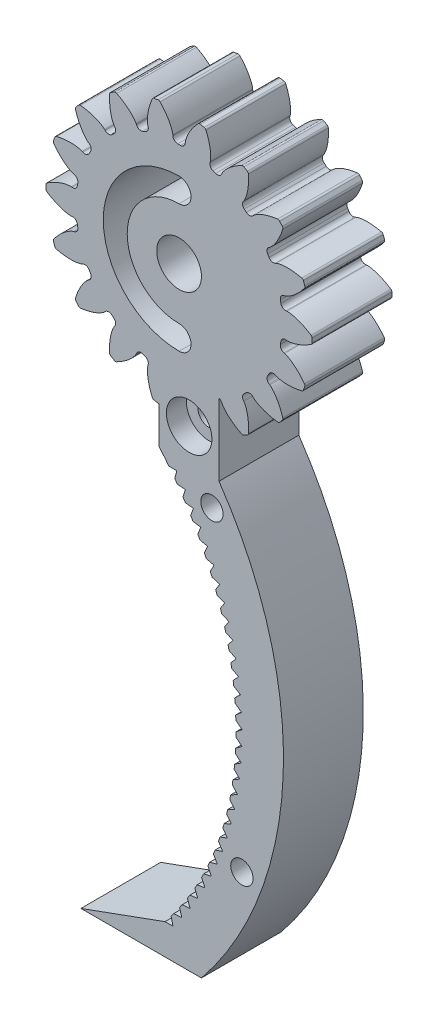
SolidWorks part; units mm, degrees
material "Alloy Steel"
ref_plane "Front" through (0, 0, 0) normal (0, 0, 1) x (1, 0, 0)
ref_plane "Top" through (0, 0, 0) normal (0, 1, 0) x (1, 0, 0)
ref_plane "Right" through (0, 0, 0) normal (1, 0, 0) x (0, 0, -1)
sketch "Sketch1" plane through (0, 0, 0) normal (0, 0, 1) x (1, 0, 0)
  circle A0 centre (0, 0) radius 21.1667
extrude "Boss-Extrude1" add sketch "Sketch1" along normal blind 12.7
sketch "Sketch3" plane through (0, 0, 0) normal (0, 0, 1) x (1, 0, 0)
  line L0 (0, 0) -> (43.7181, 0) construction
  line L2 (0, 0) -> (-0.9393, 16.3773) construction
  line L3 (0, 0) -> (0.9393, 16.3773) construction
  line L4 (0.9393, 16.3773) -> (0.9886, 17.2368) construction
  line L5 (0, 0) -> (0, 61.276) construction
  line L6 (-0.9393, 16.3773) -> (-0.9886, 17.2368) construction
  circle A0 centre (0, 0) radius 21.1667 construction
  circle A1 centre (0, 0) radius 19.05 construction
  circle A2 centre (0, 0) radius 17.2652 construction
  arc A3 (0.9393, 16.3773) -> (-0.9393, 16.3773) centre (0, 0) ccw construction
  arc A5 (3.1554, 20.9302) -> (-3.1554, 20.9302) centre (0, 0) ccw
  spline S0 degree 4 poles (-0.9886, 17.2368) (-0.9891, 17.2432) (-0.9907, 17.2612) (-0.9949, 17.295) (-1.0034, 17.35) (-1.0167, 17.4198) (-1.0366, 17.5096) (-1.0637, 17.6148) (-1.0972, 17.7297) (-1.1377, 17.8539) (-1.1816, 17.977) (-1.2287, 18.099) (-1.2785, 18.2198) (-1.3423, 18.3651) (-1.4236, 18.5381) (-1.5256, 18.738) (-1.6493, 18.9622) (-1.784, 19.1875) (-1.9235, 19.4067) (-2.0724, 19.6249) (-2.2221, 19.8338) (-2.3856, 20.0472) (-2.5406, 20.2425) (-2.7229, 20.4571) (-2.8726, 20.6291) (-3.0791, 20.8514) (-3.2038, 20.9813) (-3.3529, 21.1316) (-3.4207, 21.1975) (-3.4624, 21.2381) knots 0 0 0 0 0 0.005377 0.015084 0.028532 0.04661 0.064855 0.092111 0.119476 0.146842 0.174209 0.201575 0.228941 0.256307 0.307035 0.361767 0.4165 0.471232 0.525964 0.580697 0.635429 0.690161 0.744894 0.799626 0.854358 0.909091 0.954545 1 1 1 1 1 construction
  spline S1 degree 4 poles (-0.9886, 17.2368) (-0.9891, 17.2432) (-0.9907, 17.2612) (-0.9949, 17.295) (-1.0034, 17.35) (-1.0167, 17.4198) (-1.0366, 17.5096) (-1.0637, 17.6148) (-1.0972, 17.7297) (-1.1377, 17.8539) (-1.1816, 17.977) (-1.2287, 18.099) (-1.2785, 18.2198) (-1.3423, 18.3651) (-1.4236, 18.5381) (-1.5256, 18.738) (-1.6493, 18.9622) (-1.784, 19.1875) (-1.9235, 19.4067) (-2.0724, 19.6249) (-2.2221, 19.8338) (-2.3856, 20.0472) (-2.5406, 20.2425) (-2.7229, 20.4571) (-2.8726, 20.6291) (-3.0344, 20.8032) (-3.1141, 20.8874) (-3.1554, 20.9302) knots 0 0 0 0 0 0.005377 0.015084 0.028532 0.04661 0.064855 0.092111 0.119476 0.146842 0.174209 0.201575 0.228941 0.256307 0.307035 0.361767 0.4165 0.471232 0.525964 0.580697 0.635429 0.690161 0.744894 0.799626 0.854358 0.909091 0.909091 0.909091 0.909091 0.909091
  spline S2 degree 4 poles (0.9886, 17.2368) (0.9891, 17.2432) (0.9907, 17.2612) (0.9949, 17.295) (1.0034, 17.35) (1.0167, 17.4198) (1.0366, 17.5096) (1.0637, 17.6148) (1.0972, 17.7297) (1.1377, 17.8539) (1.1816, 17.977) (1.2287, 18.099) (1.2785, 18.2198) (1.3423, 18.3651) (1.4236, 18.5381) (1.5256, 18.738) (1.6493, 18.9622) (1.784, 19.1875) (1.9235, 19.4067) (2.0724, 19.6249) (2.2221, 19.8338) (2.3856, 20.0472) (2.5406, 20.2425) (2.7229, 20.4571) (2.8726, 20.6291) (3.0791, 20.8514) (3.2038, 20.9813) (3.3529, 21.1316) (3.4207, 21.1975) (3.4624, 21.2381) knots 0 0 0 0 0 0.005377 0.015084 0.028532 0.04661 0.064855 0.092111 0.119476 0.146842 0.174209 0.201575 0.228941 0.256307 0.307035 0.361767 0.4165 0.471232 0.525964 0.580697 0.635429 0.690161 0.744894 0.799626 0.854358 0.909091 0.954545 1 1 1 1 1 construction
  spline S3 degree 4 poles (0.9886, 17.2368) (0.9891, 17.2432) (0.9907, 17.2612) (0.9949, 17.295) (1.0034, 17.35) (1.0167, 17.4198) (1.0366, 17.5096) (1.0637, 17.6148) (1.0972, 17.7297) (1.1377, 17.8539) (1.1816, 17.977) (1.2287, 18.099) (1.2785, 18.2198) (1.3423, 18.3651) (1.4236, 18.5381) (1.5256, 18.738) (1.6493, 18.9622) (1.784, 19.1875) (1.9235, 19.4067) (2.0724, 19.6249) (2.2221, 19.8338) (2.3856, 20.0472) (2.5406, 20.2425) (2.7229, 20.4571) (2.8726, 20.6291) (3.0344, 20.8032) (3.1141, 20.8874) (3.1554, 20.9302) knots 0 0 0 0 0 0.005377 0.015084 0.028532 0.04661 0.064855 0.092111 0.119476 0.146842 0.174209 0.201575 0.228941 0.256307 0.307035 0.361767 0.4165 0.471232 0.525964 0.580697 0.635429 0.690161 0.744894 0.799626 0.854358 0.909091 0.909091 0.909091 0.909091 0.909091
  point P0 (0, 16.4042)
sketch "DCLTBC" plane through (0, 0, 0) normal (0, 0, 1) x (1, 0, 0)
  line L0 (0, 0) -> (41.04, 0) construction
  line L1 (-0.9393, 16.3773) -> (-0.9886, 17.2368) construction
  line L2 (0.9393, 16.3773) -> (0.9886, 17.2368) construction
  line L3 (-0.9393, 16.3773) -> (-0.9886, 17.2368)
  line L4 (0.9393, 16.3773) -> (0.9886, 17.2368)
  line L5 (0, 0) -> (0, 104.9356) construction
  circle A0 centre (0, 0) radius 21.1667
  circle A1 centre (0, 0) radius 19.05 construction
  circle A2 centre (0, 0) radius 17.2652 construction
  arc A3 (0.9393, 16.3773) -> (-0.9393, 16.3773) centre (0, 0) ccw construction
  arc A4 (0.9393, 16.3773) -> (-0.9393, 16.3773) centre (0, 0) ccw
  spline S0 degree 4 poles (-998.2859, -55.9585) (-15.2714, 14.5763) (-1.1564, 16.0258) (-0.9033, 16.703) (-1.0034, 17.35) (-1.0167, 17.4198) (-1.0366, 17.5096) (-1.0637, 17.6148) (-1.0972, 17.7297) (-1.1377, 17.8539) (-1.1816, 17.977) (-1.2287, 18.099) (-1.2785, 18.2198) (-1.3423, 18.3651) (-1.4236, 18.5381) (-1.5256, 18.738) (-1.6493, 18.9622) (-1.784, 19.1875) (-1.9235, 19.4067) (-2.0724, 19.6249) (-2.2221, 19.8338) (-2.3856, 20.0472) (-2.5406, 20.2425) (-2.7229, 20.4571) (-3.4042, 21.2399) (-5.6764, 23.4628) (17.3745, -0.7418) (-697.1444, 740.8893) knots -0.501613 -0.501613 -0.501613 -0.501613 -0.501613 0.005377 0.015084 0.028532 0.04661 0.064855 0.092111 0.119476 0.146842 0.174209 0.201575 0.228941 0.256307 0.307035 0.361767 0.4165 0.471232 0.525964 0.580697 0.635429 0.690161 0.744894 0.799626 0.854358 1.68661 1.68661 1.68661 1.68661 1.68661 only from (-0.9886, 17.2368) to (-3.1554, 20.9302) construction
  spline S1 degree 4 poles (998.2859, -55.9585) (15.2714, 14.5763) (1.1564, 16.0258) (0.9033, 16.703) (1.0034, 17.35) (1.0167, 17.4198) (1.0366, 17.5096) (1.0637, 17.6148) (1.0972, 17.7297) (1.1377, 17.8539) (1.1816, 17.977) (1.2287, 18.099) (1.2785, 18.2198) (1.3423, 18.3651) (1.4236, 18.5381) (1.5256, 18.738) (1.6493, 18.9622) (1.784, 19.1875) (1.9235, 19.4067) (2.0724, 19.6249) (2.2221, 19.8338) (2.3856, 20.0472) (2.5406, 20.2425) (2.7229, 20.4571) (3.4042, 21.2399) (5.6764, 23.4628) (-17.3745, -0.7418) (697.1444, 740.8893) knots -0.501613 -0.501613 -0.501613 -0.501613 -0.501613 0.005377 0.015084 0.028532 0.04661 0.064855 0.092111 0.119476 0.146842 0.174209 0.201575 0.228941 0.256307 0.307035 0.361767 0.4165 0.471232 0.525964 0.580697 0.635429 0.690161 0.744894 0.799626 0.854358 1.68661 1.68661 1.68661 1.68661 1.68661 only from (0.9886, 17.2368) to (3.1554, 20.9302) construction
  spline S2 degree 4 poles (-0.9886, 17.2368) (-0.9891, 17.2432) (-0.9907, 17.2612) (-0.9949, 17.295) (-1.0034, 17.35) (-1.0167, 17.4198) (-1.0366, 17.5096) (-1.0637, 17.6148) (-1.0972, 17.7297) (-1.1377, 17.8539) (-1.1816, 17.977) (-1.2287, 18.099) (-1.2785, 18.2198) (-1.3423, 18.3651) (-1.4236, 18.5381) (-1.5256, 18.738) (-1.6493, 18.9622) (-1.784, 19.1875) (-1.9235, 19.4067) (-2.0724, 19.6249) (-2.2221, 19.8338) (-2.3856, 20.0472) (-2.5406, 20.2425) (-2.7229, 20.4571) (-2.8726, 20.6291) (-3.0344, 20.8032) (-3.1141, 20.8874) (-3.1554, 20.9302) knots 0 0 0 0 0 0.005377 0.015084 0.028532 0.04661 0.064855 0.092111 0.119476 0.146842 0.174209 0.201575 0.228941 0.256307 0.307035 0.361767 0.4165 0.471232 0.525964 0.580697 0.635429 0.690161 0.744894 0.799626 0.854358 0.909091 0.909091 0.909091 0.909091 0.909091
  spline S3 degree 4 poles (0.9886, 17.2368) (0.9891, 17.2432) (0.9907, 17.2612) (0.9949, 17.295) (1.0034, 17.35) (1.0167, 17.4198) (1.0366, 17.5096) (1.0637, 17.6148) (1.0972, 17.7297) (1.1377, 17.8539) (1.1816, 17.977) (1.2287, 18.099) (1.2785, 18.2198) (1.3423, 18.3651) (1.4236, 18.5381) (1.5256, 18.738) (1.6493, 18.9622) (1.784, 19.1875) (1.9235, 19.4067) (2.0724, 19.6249) (2.2221, 19.8338) (2.3856, 20.0472) (2.5406, 20.2425) (2.7229, 20.4571) (2.8726, 20.6291) (3.0344, 20.8032) (3.1141, 20.8874) (3.1554, 20.9302) knots 0 0 0 0 0 0.005377 0.015084 0.028532 0.04661 0.064855 0.092111 0.119476 0.146842 0.174209 0.201575 0.228941 0.256307 0.307035 0.361767 0.4165 0.471232 0.525964 0.580697 0.635429 0.690161 0.744894 0.799626 0.854358 0.909091 0.909091 0.909091 0.909091 0.909091
extrude "Cut-Extrude-DCLTBC" cut sketch "DCLTBC" along normal through all
fillet "Fillet-Tip-DCLTBC" radius 0.3764 2 edges at (3.1554, 20.9302, 6.35) (-3.1554, 20.9302, 6.35)
fillet "Fillet-Root-DCLTBC" radius 0.7528 2 edges at (-0.9393, 16.3773, 6.35) (0.9393, 16.3773, 6.35)
pattern_circular "CirPattern-DCLTBC" count 18 over 360 about axis through (0, 0, 12.7) along (0, 0, 1) of "Cut-Extrude-DCLTBC", "Fillet-Tip-DCLTBC", "Fillet-Root-DCLTBC"
sketch "DCGTBC" [suppressed] plane through (0, 0, 0) normal (0, 0, 1) x (1, 0, 0)
  line L0 (0, 0) -> (41.04, 0) construction
  line L1 (-22.6634, 1.9828) -> (0, 0) construction
  line L2 (0, 0) -> (22.6634, 1.9828) construction
  line L3 (0, 0) -> (-16.5124, 0)
  line L5 (0, 0) -> (0, 104.9356) construction
  circle A0 centre (0, 0) radius 25
  circle A1 centre (0, 0) radius 24 construction
  circle A2 centre (0, 0) radius 21.7514 construction
  arc A3 (0.0626, 22.7499) -> (-0.0626, 22.7499) centre (0, 0) ccw construction
  arc A11 (22.6634, 1.9828) -> (-22.6634, 1.9828) centre (0, 0) ccw
  spline S4 degree 4 poles (999.7589, -2.0808) (12.8658, 20.0937) (0.2547, 20.6746) (0.0189, 21.2606) (0.0654, 21.8429) (0.0715, 21.8997) (0.0812, 21.973) (0.095, 22.0592) (0.1126, 22.1539) (0.1343, 22.2566) (0.1583, 22.3589) (0.1845, 22.4607) (0.2124, 22.562) (0.2486, 22.6844) (0.2952, 22.8308) (0.3543, 23.0013) (0.4268, 23.1939) (0.5065, 23.3893) (0.5897, 23.5809) (0.6793, 23.7735) (0.7698, 23.9592) (0.8695, 24.151) (0.9643, 24.3275) (1.0767, 24.524) (1.517, 25.277) (3.0654, 27.5692) (-13.787, 0.9944) (540.7091, 867.0187) knots -0.561807 -0.561807 -0.561807 -0.561807 -0.561807 0.005377 0.015084 0.028532 0.04661 0.064855 0.092111 0.119476 0.146842 0.174209 0.201575 0.228941 0.256307 0.307035 0.361767 0.4165 0.471232 0.525964 0.580697 0.635429 0.690161 0.744894 0.799626 0.854358 1.731906 1.731906 1.731906 1.731906 1.731906 only from (0.0598, 21.7513) to (1.3455, 24.9638) construction
  spline S5 degree 4 poles (-999.7589, -2.0808) (-12.8658, 20.0937) (-0.2547, 20.6746) (-0.0189, 21.2606) (-0.0654, 21.8429) (-0.0715, 21.8997) (-0.0812, 21.973) (-0.095, 22.0592) (-0.1126, 22.1539) (-0.1343, 22.2566) (-0.1583, 22.3589) (-0.1845, 22.4607) (-0.2124, 22.562) (-0.2486, 22.6844) (-0.2952, 22.8308) (-0.3543, 23.0013) (-0.4268, 23.1939) (-0.5065, 23.3893) (-0.5897, 23.5809) (-0.6793, 23.7735) (-0.7698, 23.9592) (-0.8695, 24.151) (-0.9643, 24.3275) (-1.0767, 24.524) (-1.517, 25.277) (-3.0654, 27.5692) (13.787, 0.9944) (-540.7091, 867.0187) knots -0.561807 -0.561807 -0.561807 -0.561807 -0.561807 0.005377 0.015084 0.028532 0.04661 0.064855 0.092111 0.119476 0.146842 0.174209 0.201575 0.228941 0.256307 0.307035 0.361767 0.4165 0.471232 0.525964 0.580697 0.635429 0.690161 0.744894 0.799626 0.854358 1.731906 1.731906 1.731906 1.731906 1.731906 only from (-0.0598, 21.7513) to (-1.3455, 24.9638) construction
  spline S6 degree 4 poles (0.0598, 21.7513) (0.0599, 21.7565) (0.0603, 21.7709) (0.0618, 21.7983) (0.0654, 21.8429) (0.0715, 21.8997) (0.0812, 21.973) (0.095, 22.0592) (0.1126, 22.1539) (0.1343, 22.2566) (0.1583, 22.3589) (0.1845, 22.4607) (0.2124, 22.562) (0.2486, 22.6844) (0.2952, 22.8308) (0.3543, 23.0013) (0.4268, 23.1939) (0.5065, 23.3893) (0.5897, 23.5809) (0.6793, 23.7735) (0.7698, 23.9592) (0.8695, 24.151) (0.9643, 24.3275) (1.0767, 24.524) (1.1693, 24.6823) (1.27, 24.8447) (1.3197, 24.9235) (1.3455, 24.9638) knots 0 0 0 0 0 0.005377 0.015084 0.028532 0.04661 0.064855 0.092111 0.119476 0.146842 0.174209 0.201575 0.228941 0.256307 0.307035 0.361767 0.4165 0.471232 0.525964 0.580697 0.635429 0.690161 0.744894 0.799626 0.854358 0.909091 0.909091 0.909091 0.909091 0.909091
  spline S7 degree 4 poles (-0.0598, 21.7513) (-0.0599, 21.7565) (-0.0603, 21.7709) (-0.0618, 21.7983) (-0.0654, 21.8429) (-0.0715, 21.8997) (-0.0812, 21.973) (-0.095, 22.0592) (-0.1126, 22.1539) (-0.1343, 22.2566) (-0.1583, 22.3589) (-0.1845, 22.4607) (-0.2124, 22.562) (-0.2486, 22.6844) (-0.2952, 22.8308) (-0.3543, 23.0013) (-0.4268, 23.1939) (-0.5065, 23.3893) (-0.5897, 23.5809) (-0.6793, 23.7735) (-0.7698, 23.9592) (-0.8695, 24.151) (-0.9643, 24.3275) (-1.0767, 24.524) (-1.1693, 24.6823) (-1.27, 24.8447) (-1.3197, 24.9235) (-1.3455, 24.9638) knots 0 0 0 0 0 0.005377 0.015084 0.028532 0.04661 0.064855 0.092111 0.119476 0.146842 0.174209 0.201575 0.228941 0.256307 0.307035 0.361767 0.4165 0.471232 0.525964 0.580697 0.635429 0.690161 0.744894 0.799626 0.854358 0.909091 0.909091 0.909091 0.909091 0.909091
  dimension "D1" = 5
  dimension "D2" = 5
extrude "Cut-Extrude-DCGTBC" [suppressed] cut sketch "DCGTBC" along normal through all
fillet "Fillet-Tip-DCGTBC" [suppressed] radius 0.3764
pattern_circular "CirPattern-DCGTBC" [suppressed] count 18 over 360
sketch "Sketch4" plane through (0, 0, 12.7) normal (0, 0, 1) x (1, 0, 0)
  circle A1 centre (0, 0) radius 3.556
  dimension "D1" = 7.112
extrude "Cut-Extrude2" cut sketch "Sketch4" against normal through all
sketch "Sketch5" plane through (0, 0, 12.7) normal (0, 0, 1) x (1, 0, 0)
  circle A0 centre (-7, 0) radius 1
  circle A1 centre (0, 7) radius 1
  circle A2 centre (7, 0) radius 1
  circle A3 centre (0, -7) radius 1
  point P12 (0, 0)
  dimension "D2" = 2
  dimension "D1" = 7
  dimension "D3" = 4
extrude "Cut-Extrude3" [suppressed] cut sketch "Sketch5" against normal through all
sketch "Sketch7" plane through (0, 0, 12.7) normal (0, 0, 1) x (1, 0, 0)
  line L0 (6.35, -14.1137) -> (6.35, -26.8137)
  line L2 (-3.175, -26.8137) -> (-3.175, -14.1137)
  line L3 (-3.175, -14.1137) -> (6.35, -14.1137)
  line L4 (-2.2365, -91.7884) -> (-15.6293, -96.6637)
  line L5 (-15.6293, -96.6637) -> (3.5477, -96.6637)
  arc A0 (-3.175, -26.8137) -> (-2.2365, -91.7884) centre (-41.7528, -59.8651) cw
  arc A1 (6.35, -26.8137) -> (3.5477, -96.6637) centre (-41.7528, -59.8651) cw
  dimension "D3" = 50.8
  dimension "D1" = 9.525
  dimension "D2" = 12.7
  dimension "D4" = 82.55
  dimension "D5" = 3.175
  dimension "D6" = 77.6747
  dimension "D7" = 19.177
extrude "Boss-Extrude3" add sketch "Sketch7" against normal through all
sketch "Sketch9" plane through (0, 0, 12.7) normal (0, 0, 1) x (1, 0, 0)
  circle A0 centre (5.2228, -31.0331) radius 1.778
  arc A1 (3.5477, -96.6637) -> (6.35, -26.8137) centre (-41.7528, -59.8651) ccw construction
  circle A2 centre (9.9936, -78.8467) radius 1.778
  arc A3 (-2.2365, -91.7884) -> (-3.175, -26.8137) centre (-41.7528, -59.8651) ccw construction
  dimension "D1" = 3.556
  dimension "D2" = 55.118
  dimension "D3" = 3.556
  dimension "D4" = 55.118
extrude "Cut-Extrude4" cut sketch "Sketch9" against normal blind 101.6
sketch "Sketch10" [suppressed] plane through (0, 0, 12.7) normal (0, 0, 1) x (1, 0, 0)
  circle A0 centre (-7, 0) radius 2.75
  circle A1 centre (0, -7) radius 2.75
  circle A2 centre (7, 0) radius 2.75
  circle A3 centre (0, 7) radius 2.75
  dimension "D1" = 5.5
extrude "Cut-Extrude5" [suppressed] cut sketch "Sketch10" against normal blind 7.7
sketch "Sketch11" plane through (0, 0, 12.7) normal (0, 0, 1) x (1, 0, 0)
  line L0 (-2.2365, -91.7884) -> (-0.9665, -91.7884)
  line L1 (-0.9665, -91.7884) -> (-1.2716, -90.5556)
  arc A0 (-2.2365, -91.7884) -> (-3.175, -26.8137) centre (-41.7528, -59.8651) ccw construction
  arc A1 (-2.2365, -91.7884) -> (-1.2716, -90.5556) centre (-41.7528, -59.8651) ccw
  dimension "D1" = 1.27
  dimension "D2" = 1.27
extrude "Cut-Extrude6" cut sketch "Sketch11" against normal through all
pattern_circular "CirPattern1" count 30 over 75 about axis through (-41.7528, -59.8651, 0) along (0, 0, 1) of "Cut-Extrude6"
sketch "Sketch12" plane through (0, 0, 12.7) normal (0, 0, 1) x (1, 0, 0)
  arc A0 (0, -10.16) -> (0, 10.16) centre (0, 0) cw construction
  arc A1 (0, 12.065) -> (0, -12.065) centre (0, 0) ccw
  arc A2 (0, 8.255) -> (0, -8.255) centre (0, 0) ccw
  arc A3 (0, 8.255) -> (0, 12.065) centre (0, 10.16) ccw
  arc A4 (0, -12.065) -> (0, -8.255) centre (0, -10.16) ccw
  point P4 (-10.16, 0)
  dimension "D1" = 3.81
  dimension "D2" = 10.16
extrude "Cut-Extrude7" cut sketch "Sketch12" against normal blind 12.7
sketch "Sketch13" plane through (0, 0, 12.7) normal (0, 0, 1) x (1, 0, 0)
  line L0 (-3.175, -20.8853) -> (-3.175, -26.8137) construction
  circle A0 centre (1.6002, -21.59) radius 1.778
  point P4 (-3.175, -23.8495)
  dimension "D1" = 3.556
  dimension "D2" = 4.7752
  dimension "D3" = 21.59
extrude "Cut-Extrude8" cut sketch "Sketch13" against normal blind 12.7
sketch "Sketch14" plane through (0, 0, 12.7) normal (0, 0, 1) x (1, 0, 0)
  circle A0 centre (1.6002, -21.59) radius 3.6195
  dimension "D1" = 7.239
extrude "Cut-Extrude9" cut sketch "Sketch14" against normal blind 3.175
sketch "Sketch15" plane through (0, 0, 0) normal (0, 0, -1) x (-1, 0, 0)
  circle A0 centre (-1.6002, -21.59) radius 3.6195
  dimension "D1" = 7.239
extrude "Cut-Extrude10" cut sketch "Sketch15" against normal blind 3.175
equation "\"DiametralPitch\"= 12'Diametral Pitch"
equation "\"NumTeeth\"= 18'Number of Teeth"
equation "\"PressureAngle\"= 25deg'Pressure Angle"
equation "\"Addendum\"= 1 / \"DiametralPitch\"'Addendum"
equation "\"Dedendum\"= 1.25 / \"DiametralPitch\"'Dedendum"
equation "\"WorkingDepth\"= 2 / \"DiametralPitch\"'Working Depth - here for REF (Not used in building model)"
equation "\"WholeDepth\"= 2.25 / \"DiametralPitch\"'Whole Depth - here for REF (Not used in building model)"
equation "\"Clearance\"= .25 / \"DiametralPitch\"'Clearance"
equation "\"CircularPitch\"= pi / \"DiametralPitch\"'Circular Pitch - here for REF (Not used in building model)"
equation "\"PitchCircle\"= \"NumTeeth\" / \"DiametralPitch\"'Pitch Circle - or - Pitch Diameter"
equation "\"OutsideDiameter\"= ( \"NumTeeth\" + 2 ) / \"DiametralPitch\"'Outside Diameter"
equation "\"Fillet_Root\"= \"Clearance\" * cos ( \"PressureAngle\" ) * tan ( ( 90 + \"PressureAngle\" ) / 2 ) 'Fillet Root"
equation "\"AddendumCircle\"= \"PitchCircle\" + ( 2 * \"Addendum\" )'Addendum Circle - or - Addendum Diameter"
equation "\"DedendumCircle\"= \"PitchCircle\" - ( 2 * \"Dedendum\" )'Dedendum Circle - or - Dedendum Diameter"
equation "\"BaseCircle\"= \"PitchCircle\" * cos ( \"PressureAngle\" )'Base Circle - Base Diameter"
equation "\"PitchAngle\"= 360deg / \"NumTeeth\"'Pitch Angle"
equation "\"Alpha\"= sqr ( \"PitchCircle\" ^ 2 - \"BaseCircle\" ^ 2 ) / \"BaseCircle\" * 180 / PI - \"PressureAngle\"'Alpha - Used for Calculating Beta"
equation "\"Beta\"= ( \"PitchAngle\" / 4 - ( \"Alpha\" - 90 ) )'Beta - Used in definition of the parameters for the parametric equation driven curve"
equation "\"Gamma\"= ( \"PitchAngle\" / 4 - ( \"Alpha\" + 90 ) )'Gamma - Used in definition of the parameters for the parametric equation driven curve"
equation "\"Phi\"= sqr ( ( \"AddendumCircle\" / 2 ) ^ 2 - ( \"BaseCircle\" / 2 ) ^ 2 ) / ( \"BaseCircle\" / 2 )'Phi - Used in definition of the parameters for the parametric equation driven curve"
equation "\"DCGTBC\"= iif ( \"DedendumCircle\" > \"BaseCircle\" , \"unsuppressed\" , \"suppressed\" )'if Dedendum Circle IS GREATER THAN BaseCircle THEN UnsuppressORSuppress FEATURE"
equation "\"DCLTBC\"= iif ( \"DedendumCircle\" - .002 > \"BaseCircle\" , \"suppressed\" , \"unsuppressed\" )'if Dedendum Circle - .002 IS GREATER THAN BaseCircle THEN SuppressORUnsuppress FEATURE"
equation "\"Cut-Extrude-DCGTBC\"= iif ( \"DedendumCircle\" > \"BaseCircle\" , \"unsuppressed\" , \"suppressed\" )'if Dedendum Circle IS GREATER THAN BaseCircle THEN UnsuppressORSuppress FEATURE"
equation "\"Cut-Extrude-DCLTBC\"= iif ( \"DedendumCircle\" - .002 > \"BaseCircle\" , \"suppressed\" , \"unsuppressed\" )'if Dedendum Circle - .002 IS GREATER THAN BaseCircle THEN SuppressORUnsuppress FEATURE"
equation "\"CirPattern-DCGTBC\"= iif ( \"DedendumCircle\" > \"BaseCircle\" , \"unsuppressed\" , \"suppressed\" )'if Dedendum Circle IS GREATER THAN BaseCircle THEN UnsuppressORSuppress FEATURE"
equation "\"CirPattern-DCLTBC\"= iif ( \"DedendumCircle\" - .002 > \"BaseCircle\" , \"suppressed\" , \"unsuppressed\" )'if Dedendum Circle - .002 IS GREATER THAN BaseCircle THEN SuppressORUnsuppress FEATURE"
equation "\"Fillet-Tip-DCGTBC\"= iif ( \"DedendumCircle\" > \"BaseCircle\" , \"unsuppressed\" , \"suppressed\" )'if Dedendum Circle IS GREATER THAN BaseCircle THEN UnsuppressORSuppress FEATURE"
equation "\"Fillet-Tip-DCLTBC\"= iif ( \"DedendumCircle\" - .002 > \"BaseCircle\" , \"suppressed\" , \"unsuppressed\" )'if Dedendum Circle - .002 IS GREATER THAN BaseCircle THEN SuppressORUnsuppress FEATURE"
equation "\"Fillet-Root-DCLTBC\"= iif ( \"DedendumCircle\" - .002 > \"BaseCircle\" , \"suppressed\" , \"unsuppressed\" )'if Dedendum Circle - .002 IS GREATER THAN BaseCircle THEN SuppressORUnsuppress FEATURE"
equation "\"D1@CirPattern-DCGTBC\"= \"NumTeeth\"'Number of Teeth"
equation "\"D1@CirPattern-DCLTBC\"= \"NumTeeth\"'Number of Teeth"
equation "\"D1@Fillet-Tip-DCGTBC\"= \"Fillet_Root\" / 2 'Tip Rad For Large No of Teeth"
equation "\"D1@Fillet-Tip-DCLTBC\"=\"Fillet_Root\" / 2'Tip Rad For Small No of Teeth"
equation "\"D1@Fillet-Root-DCLTBC\"= \"Fillet_Root\"'Fillet Root"
